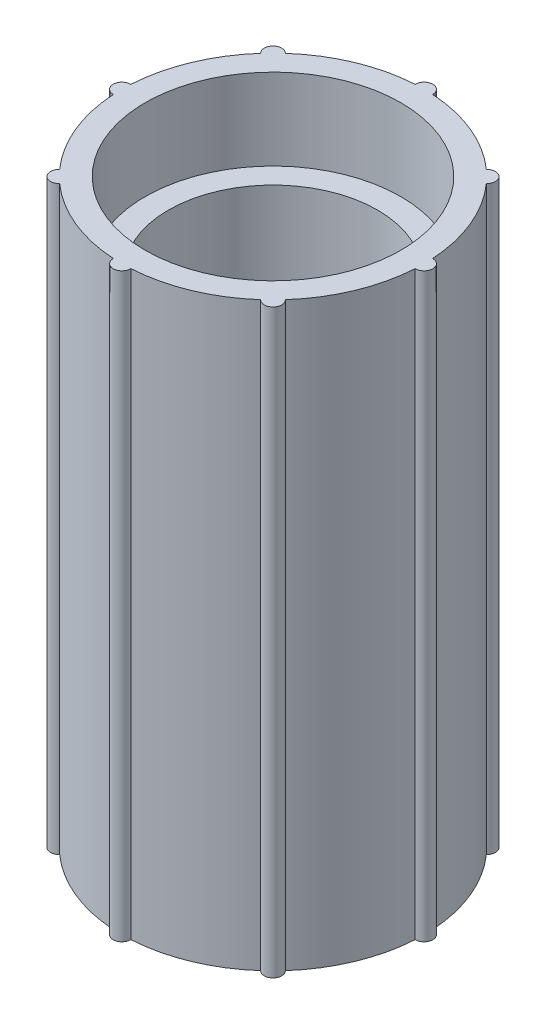
SolidWorks part; units mm, degrees
ref_plane "Plan de face" through (0, 0, 0) normal (0, 0, 1) x (1, 0, 0)
ref_plane "Plan de dessus" through (0, 0, 0) normal (0, 1, 0) x (1, 0, 0)
ref_plane "Plan de droite" through (0, 0, 0) normal (1, 0, 0) x (0, 0, -1)
sketch "Esquisse2" plane through (0, 0, 0) normal (0, 1, 0) x (1, 0, 0)
  circle A0 centre (0, 0) radius 13
  dimension "D1" = 26
extrude "Boss.-Extru.1" add sketch "Esquisse2" along normal blind 25
sketch "Esquisse3" plane through (0, 0, 0) normal (0, -1, 0) x (1, 0, 0)
  circle A0 centre (0, 0) radius 9
  dimension "D1" = 18
extrude "Enlèv. mat.-Extru.1" cut sketch "Esquisse3" against normal through all
sketch "Esquisse4" plane through (0, 0, 0) normal (0, -1, 0) x (1, 0, 0)
  circle A0 centre (0, 0) radius 11
  dimension "D1" = 22
extrude "Enlèv. mat.-Extru.2" cut sketch "Esquisse4" against normal blind 7
sketch "Esquisse6" plane through (0, 0, 0) normal (0, -1, 0) x (-1, 0, 0)
  circle A0 centre (-13, 0) radius 0.75
  circle A1 centre (0, 0) radius 13 construction
  dimension "D1" = 1.5
extrude "Boss.-Extru.2" add sketch "Esquisse6" against normal blind 25 contours A0
pattern_circular "Répétition circulaire1" count 8 over 360 about axis through (0, 0, 0) along (0, 1, 0) of "Boss.-Extru.2"
mirror "Symétrie2" about plane through (0, 25, 0) normal (0, 1, 0) of "Enlèv. mat.-Extru.1", "Boss.-Extru.1", "Enlèv. mat.-Extru.2", "Boss.-Extru.2", "Répétition circulaire1"
ref_plane "Plan1" through (0, 25, 0) normal (0, 1, 0) x (1, 0, 0)
sketch "Esquisse7" plane through (0, 25, 0) normal (0, 1, 0) x (1, 0, 0)
  circle A0 centre (0, 0) radius 13.755 construction
  dimension "D1" = 27.51
